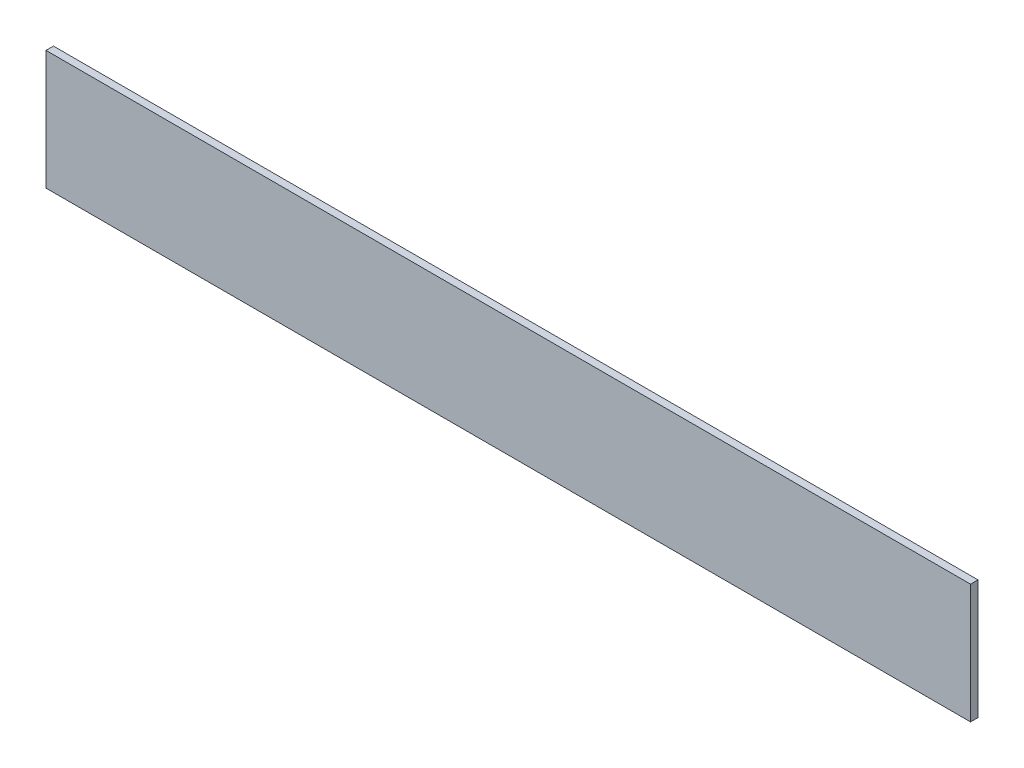
SolidWorks part; units mm, degrees
ref_plane "Front Plane" through (0, 0, 0) normal (0, 0, 1) x (1, 0, 0)
ref_plane "Top Plane" through (0, 0, 0) normal (0, 1, 0) x (1, 0, 0)
ref_plane "Right Plane" through (0, 0, 0) normal (1, 0, 0) x (0, 0, -1)
sketch "Sketch1" plane through (0, 0, 0) normal (0, 0, 1) x (1, 0, 0)
  line L1 (0, 0) -> (393.7, 0)
  line L2 (0, 0) -> (0, 50.8)
  line L3 (0, 50.8) -> (393.7, 50.8)
  line L4 (393.7, 0) -> (393.7, 50.8)
  dimension "D1" = 50.8
  dimension "D2" = 393.7
extrude "Boss-Extrude1" add sketch "Sketch1" along normal blind 3.175
